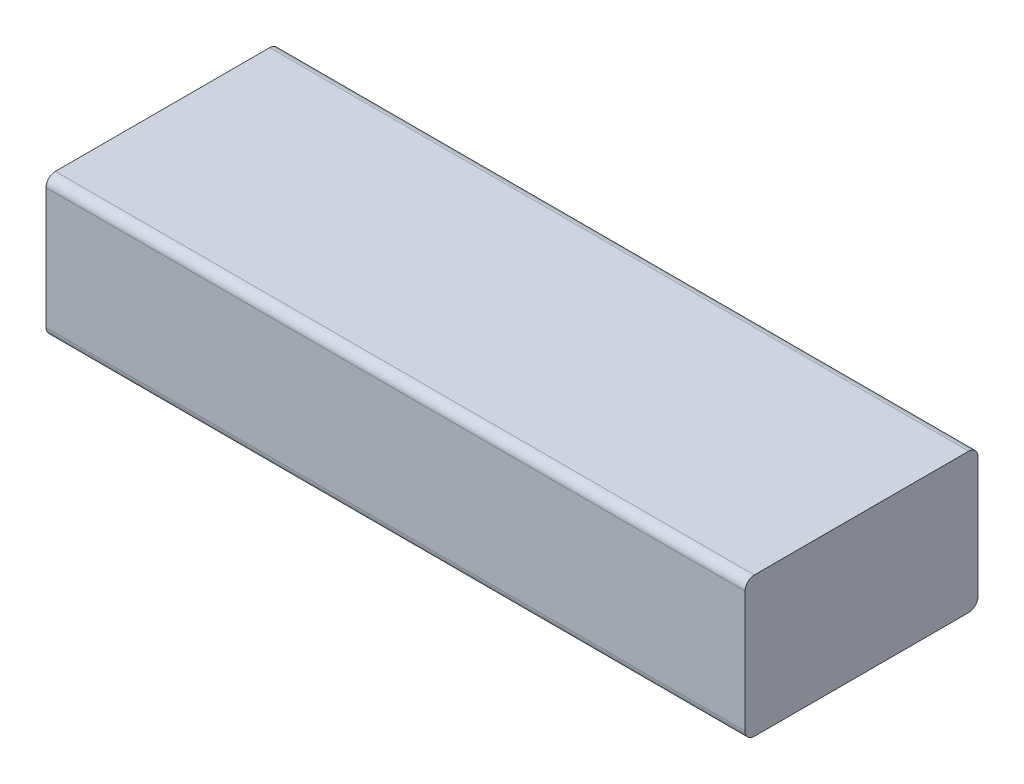
SolidWorks part; units mm, degrees
ref_plane "Ebene vorne" through (0, 0, 0) normal (0, 0, 1) x (1, 0, 0)
ref_plane "Ebene oben" through (0, 0, 0) normal (0, 1, 0) x (1, 0, 0)
ref_plane "Ebene rechts" through (0, 0, 0) normal (1, 0, 0) x (0, 0, -1)
sketch "Sketch1" plane through (0, 0, 0) normal (0, 1, 0) x (1, 0, 0)
  line L1 (-23.9286, 17.0536) -> (51.0714, 17.0536)
  line L2 (-23.9286, 17.0536) -> (-23.9286, -7.9464)
  line L3 (-23.9286, -7.9464) -> (51.0714, -7.9464)
  line L4 (51.0714, 17.0536) -> (51.0714, -7.9464)
  dimension "D1" = 25
  dimension "D2" = 75
extrude "Boss-Extrude1" add sketch "Sketch1" along normal blind 15
fillet "Fillet1" radius 1 4 edges at (13.5714, 15, -17.0536) (13.5714, 0, -17.0536) (13.5714, 0, 7.9464) (13.5714, 15, 7.9464)
